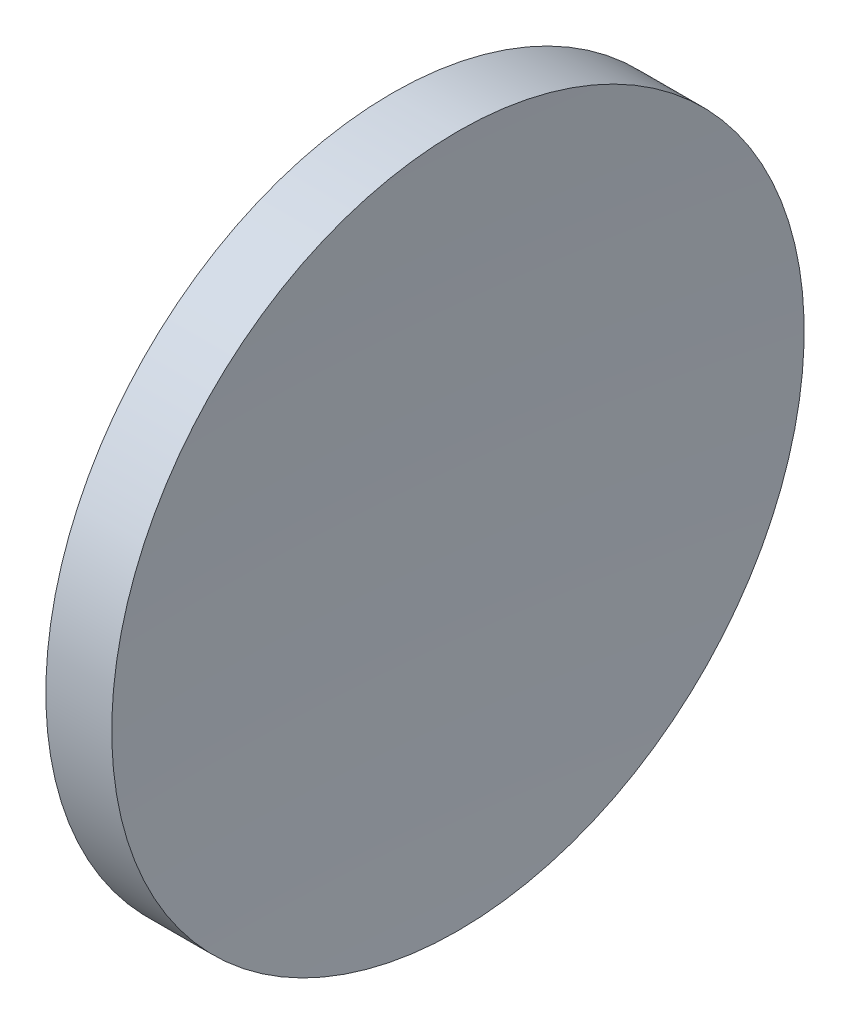
SolidWorks part; units mm, degrees
ref_plane "前视基准面" through (0, 0, 0) normal (0, 0, 1) x (1, 0, 0)
ref_plane "上视基准面" through (0, 0, 0) normal (0, 1, 0) x (1, 0, 0)
ref_plane "右视基准面" through (0, 0, 0) normal (1, 0, 0) x (0, 0, -1)
sketch "草图1" plane through (0, 0, 0) normal (0, 0, 1) x (1, 0, 0)
  line L0 (55.0074, 32.5787) -> (64.0943, 32.5787) construction
  line L1 (57.3582, 32.5787) -> (57.3582, 45.0787)
  line L2 (59.3582, 32.5787) -> (57.3582, 32.5787)
  line L3 (57.3582, 45.0787) -> (59.7376, 45.0787)
  arc A0 (59.7376, 45.0787) -> (59.3582, 32.5787) centre (265.4582, 32.5787) ccw
revolve "旋转1" add sketch "草图1" angle 360 about L0
